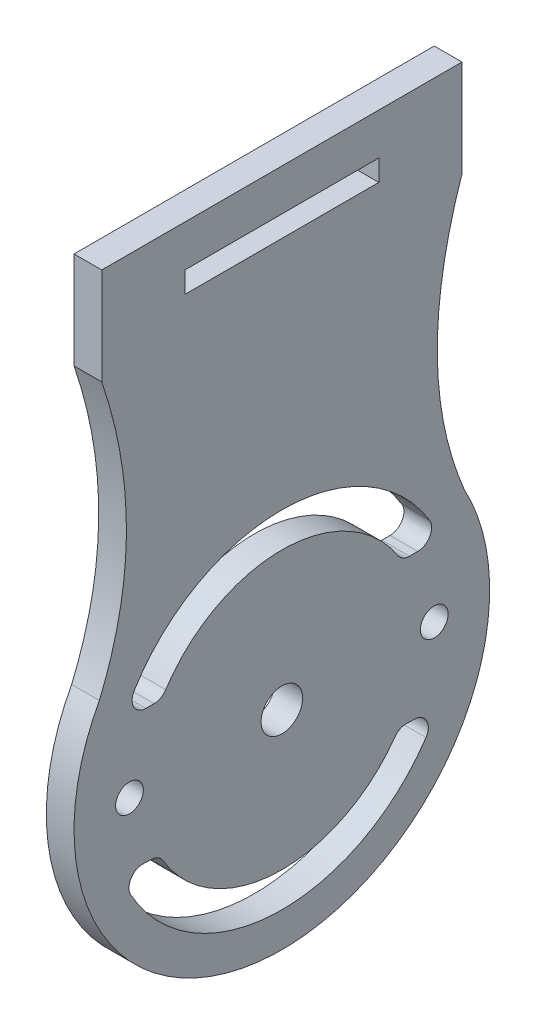
SolidWorks part; units mm, degrees
material "Plástico personalizado"
ref_plane "Plano frontal" through (0, 0, 0) normal (0, 0, 1) x (1, 0, 0)
ref_plane "Plano superior" through (0, 0, 0) normal (0, 1, 0) x (1, 0, 0)
ref_plane "Plano direito" through (0, 0, 0) normal (1, 0, 0) x (0, 0, -1)
sketch "Esboço1" plane through (0, 0, 0) normal (1, 0, 0) x (0, 0, -1)
  line L0 (-13, 34) -> (0, 34)
  line L2 (-13, 34) -> (-13, 27)
  line L3 (0, 34) -> (0, -15)
  arc A0 (-13.174, 7.1726) -> (0, -15) centre (0, 0) ccw
  spline S0 degree 2 poles (-13, 27) (-9.3542, 16.24) (-13.174, 7.1726) knots 0 0 0 0.912496 0.912496 0.912496
  dimension "D1" = 30
  dimension "D3" = 34
  dimension "D4" = 7
extrude "Ressalto-extrusão1" add sketch "Esboço1" along normal blind 2
mirror "Espelhar1" about plane through (2, 34, 0) normal (0, 0, 1) of "Ressalto-extrusão1"
sketch "Esboço2" plane through (2, 0, 0) normal (1, 0, 0) x (0, 0, -1)
  line L0 (13, 34) -> (-13, 34) construction
  line L1 (-7, 31) -> (7, 31)
  line L2 (-7, 31) -> (-7, 29.4721)
  line L3 (-7, 29.4721) -> (7, 29.4721)
  line L4 (7, 31) -> (7, 29.4721)
  line L5 (-7, 31) -> (7, 29.4721) construction
  line L6 (-7, 29.4721) -> (7, 31) construction
  line L7 (-9.8107, 5) -> (-9.2195, 5)
  line L8 (9.2195, 5) -> (9.8107, 5)
  line L9 (-9.9967, -4.6168) -> (-9.406, -4.6397)
  line L10 (9.0193, -5.3528) -> (9.61, -5.3757)
  arc A0 (10.6638, 6.5217) -> (-10.6638, 6.5217) centre (0, 0) ccw
  arc A1 (8.3814, 5.4545) -> (-8.3814, 5.4545) centre (0, 0) ccw
  arc A2 (-8.5861, -5.1263) -> (8.1642, -5.7746) centre (0, 0) ccw
  arc A3 (-10.9081, -6.1045) -> (10.4036, -6.9293) centre (0, 0) ccw
  arc A4 (-8.5861, -5.1263) -> (-9.406, -4.6397) centre (-9.4447, -5.639) ccw
  arc A5 (-9.9967, -4.6168) -> (-10.9081, -6.1045) centre (-10.0354, -5.6161) ccw
  arc A6 (10.4036, -6.9293) -> (9.61, -5.3757) centre (9.5713, -6.3749) ccw
  arc A7 (9.0193, -5.3528) -> (8.1642, -5.7746) centre (8.9806, -6.3521) ccw
  arc A8 (9.2195, 5) -> (8.3814, 5.4545) centre (9.2195, 6) cw
  arc A9 (9.8107, 5) -> (10.6638, 6.5217) centre (9.8107, 6) ccw
  arc A10 (-9.2195, 5) -> (-8.3814, 5.4545) centre (-9.2195, 6) ccw
  arc A11 (-9.8107, 5) -> (-10.6638, 6.5217) centre (-9.8107, 6) cw
  circle A12 centre (0, 0) radius 1.5
  circle A13 centre (11, 0) radius 1
  circle A14 centre (-11, 0) radius 1
  point P0 (0, 30.2361)
  point P21 (-11.6412, -4.5532)
  point P26 (8.4604, -5.3312)
  dimension "D3" = 25
  dimension "D4" = 20
  dimension "D7" = 1
  dimension "D8" = 3
  dimension "D9" = 2
  dimension "D11" = 2
  dimension "D1" = 3
  dimension "D2" = 14
  dimension "D5" = 5
  dimension "D6" = 5
  dimension "D10" = 11
  dimension "D12" = 11
extrude "Corte-extrusão1" cut sketch "Esboço2" against normal through all
